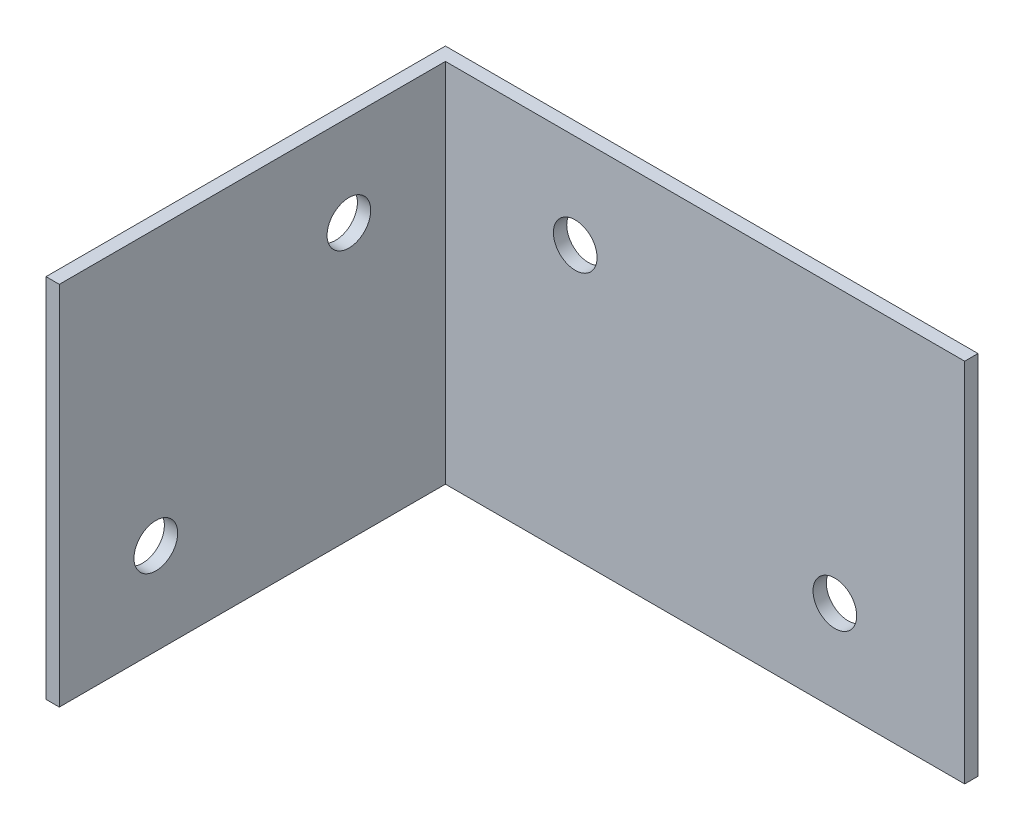
SolidWorks part; units mm, degrees
material "AISI 1020"
ref_plane "Front Plane" through (0, 0, 0) normal (0, 0, 1) x (1, 0, 0)
ref_plane "Top Plane" through (0, 0, 0) normal (0, 1, 0) x (1, 0, 0)
ref_plane "Right Plane" through (0, 0, 0) normal (1, 0, 0) x (0, 0, -1)
sketch "Sketch1" plane through (0, 0, 0) normal (0, 0, 1) x (1, 0, 0)
  line L1 (25.4, 17.4625) -> (-25.4, 17.4625)
  line L2 (25.4, 17.4625) -> (25.4, -17.4625)
  line L3 (25.4, -17.4625) -> (-25.4, -17.4625)
  line L4 (-25.4, 17.4625) -> (-25.4, -17.4625)
  line L5 (25.4, 17.4625) -> (-25.4, -17.4625) construction
  line L6 (25.4, -17.4625) -> (-25.4, 17.4625) construction
  point P0 (0, 0)
  dimension "D1" = 34.925
  dimension "D2" = 50.8
extrude "Boss-Extrude1" add sketch "Sketch1" along normal blind 1.27
sketch "Sketch2" plane through (0, 0, 1.27) normal (0, 0, 1) x (1, 0, 0)
  line L0 (-25.4, -17.4625) -> (25.4, -17.4625) construction
  line L1 (-25.4, 17.4625) -> (-24.13, 17.4625)
  line L2 (-25.4, 17.4625) -> (-25.4, -17.4625)
  line L3 (-25.4, -17.4625) -> (-24.13, -17.4625)
  line L4 (-24.13, 17.4625) -> (-24.13, -17.4625)
  dimension "D1" = 1.27
extrude "Boss-Extrude2" add sketch "Sketch2" along normal blind 36.83 contours L2 L1 L4 L3
sketch "Sketch3" plane through (-24.13, 0, 0) normal (1, 0, 0) x (0, 0, -1)
  line L0 (-38.1, 17.4625) -> (-38.1, -17.4625) construction
  line L2 (-1.27, 17.4625) -> (-1.27, -17.4625) construction
  line L3 (-38.1, -17.4625) -> (-1.27, -17.4625) construction
  line L4 (-38.1, 17.4625) -> (-1.27, 17.4625) construction
  circle A0 centre (-10.4775, 8.7312) radius 2.0828
  circle A1 centre (-28.8925, -8.7312) radius 2.0828
  dimension "D3" = 4.1656
  dimension "D4" = 4.1656
  dimension "D5" = 8.7312
  dimension "D6" = 8.7312
  dimension "D1" = 9.2075
  dimension "D2" = 9.2075
extrude "Cut-Extrude1" cut sketch "Sketch3" against normal blind 36.83
sketch "Sketch4" plane through (0, 0, 1.27) normal (0, 0, 1) x (1, 0, 0)
  line L1 (25.4, 17.4625) -> (-24.13, 17.4625) construction
  line L2 (-24.13, -17.4625) -> (25.4, -17.4625) construction
  line L3 (-24.13, 17.4625) -> (-24.13, -17.4625) construction
  line L4 (25.4, -17.4625) -> (25.4, 17.4625) construction
  circle A0 centre (-11.7475, 8.4773) radius 2.0828
  circle A1 centre (13.0175, -8.7313) radius 2.0828
  dimension "D1" = 4.1656
  dimension "D2" = 4.1656
  dimension "D3" = 8.9853
  dimension "D4" = 8.7312
  dimension "D5" = 12.3825
  dimension "D6" = 12.3825
extrude "Cut-Extrude2" cut sketch "Sketch4" against normal blind 36.83
